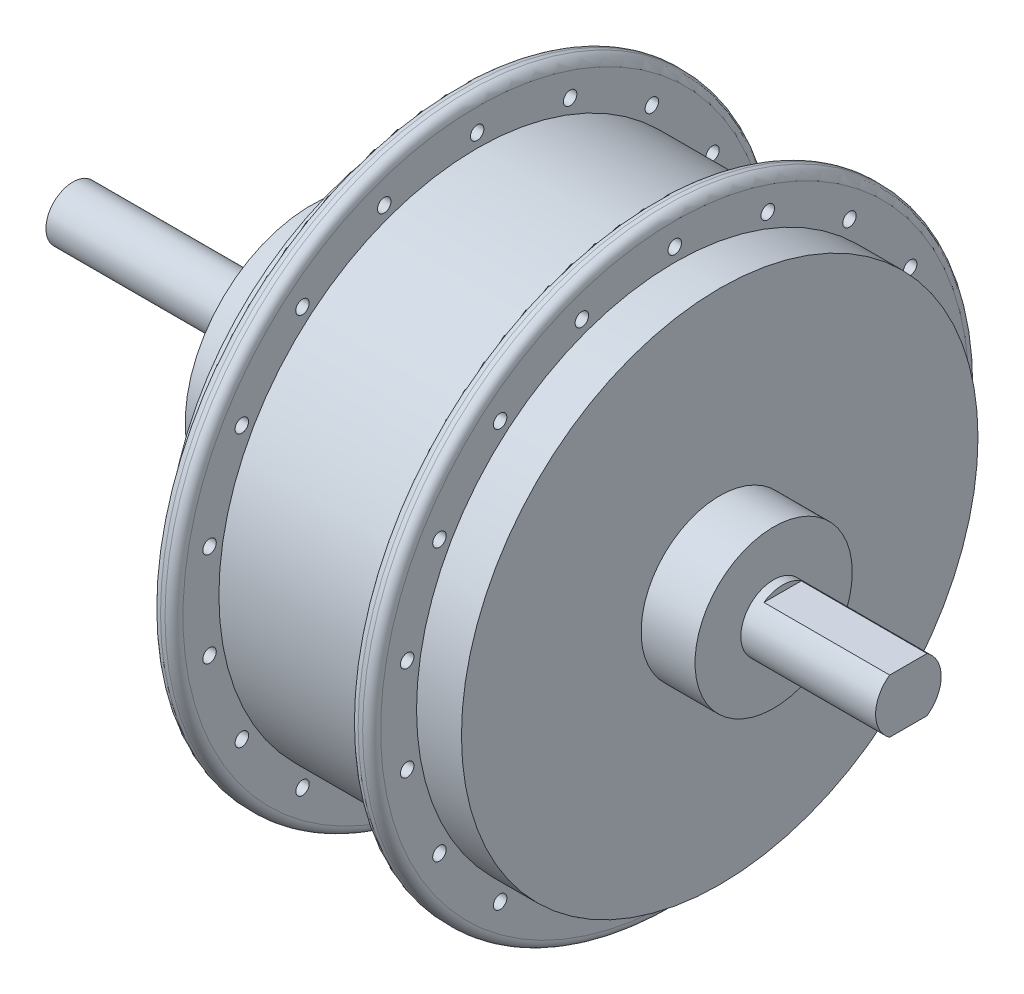
SolidWorks part; units mm, degrees
ref_plane "Спереди" through (0, 0, 0) normal (0, 0, 1) x (1, 0, 0)
ref_plane "Сверху" through (0, 0, 0) normal (0, 1, 0) x (1, 0, 0)
ref_plane "Справа" through (0, 0, 0) normal (1, 0, 0) x (0, 0, -1)
sketch "Эскиз1" plane through (0, 0, 0) normal (0, 0, 1) x (1, 0, 0)
  line L0 (27.6357, 0) -> (-114.9378, 0) construction
  line L1 (0, 0) -> (0, 7.3)
  line L2 (0, 7.3) -> (-30, 7.3)
  line L3 (-30, 7.3) -> (-30, 17.5)
  line L4 (-30, 17.5) -> (-42, 17.5)
  line L5 (-42, 17.5) -> (-42, 57.5)
  line L6 (-52, 67.5) -> (-57, 67.5)
  line L7 (-57, 67.5) -> (-57, 57.5)
  line L8 (-57, 57.5) -> (-96, 57.5)
  line L9 (-96, 57.5) -> (-96, 67.5)
  line L10 (-96, 67.5) -> (-101, 67.5)
  line L11 (-101, 67.5) -> (-101, 56)
  line L12 (-101, 56) -> (-109, 56)
  line L13 (-109, 56) -> (-109, 50)
  line L14 (-109, 50) -> (-121, 38)
  line L15 (-121, 38) -> (-121, 28)
  line L16 (-121, 28) -> (-133, 28)
  line L17 (-133, 28) -> (-133, 6)
  line L18 (-133, 6) -> (-186, 6)
  line L19 (-186, 6) -> (-186, 0)
  line L20 (-186, 0) -> (0, 0)
  line L21 (-52, 67.5) -> (-52, 57.5)
  line L22 (-52, 57.5) -> (-42, 57.5)
  point P24 (-101, 61.75)
  dimension "D1" = 14.6
  dimension "D2" = 35
  dimension "D3" = 135
  dimension "D4" = 10
  dimension "D5" = 112
  dimension "D6" = 100
  dimension "D7" = 76
  dimension "D8" = 56
  dimension "D9" = 12
  dimension "D10" = 59
  dimension "D11" = 5
  dimension "D12" = 103
  dimension "D13" = 12
  dimension "D14" = 53
  dimension "D15" = 10
  dimension "D16" = 8
  dimension "D17" = 12
  dimension "D18" = 12
  dimension "D19" = 30
  dimension "D20" = 67
  dimension "D21" = 79
  dimension "D22" = 10
  dimension "D23" = 5
revolve "Повернуть1" add sketch "Эскиз1" angle 360 about L0
fillet "Скругление1" radius 2 4 edges at (-101, 0, -67.5) (-96, 0, -67.5) (-57, 0, -67.5) (-52, 0, -67.5)
sketch "Эскиз2" plane through (-101, 0, 0) normal (-1, 0, 0) x (0, 0, 1)
  circle A0 centre (0, 60.5) radius 1.5
  circle A1 centre (20.6922, 56.8514) radius 1.5
  circle A2 centre (38.8887, 46.3457) radius 1.5
  circle A3 centre (52.3945, 30.25) radius 1.5
  circle A4 centre (59.5809, 10.5057) radius 1.5
  circle A5 centre (59.5809, -10.5057) radius 1.5
  circle A6 centre (52.3945, -30.25) radius 1.5
  circle A7 centre (38.8887, -46.3457) radius 1.5
  circle A8 centre (20.6922, -56.8514) radius 1.5
  circle A9 centre (0, -60.5) radius 1.5
  circle A10 centre (-20.6922, -56.8514) radius 1.5
  circle A11 centre (-38.8887, -46.3457) radius 1.5
  circle A12 centre (-52.3945, -30.25) radius 1.5
  circle A13 centre (-59.5809, -10.5057) radius 1.5
  circle A14 centre (-59.5809, 10.5057) radius 1.5
  circle A15 centre (-52.3945, 30.25) radius 1.5
  circle A16 centre (-38.8887, 46.3457) radius 1.5
  circle A17 centre (-20.6922, 56.8514) radius 1.5
  point P41 (0, 0)
  dimension "D2" = 3
  dimension "D1" = 59
  dimension "D3" = 18
extrude "Вырез-Вытянуть1" cut sketch "Эскиз2" against normal through all
sketch "Эскиз3" plane through (0, 0, 0) normal (1, 0, 0) x (0, 0, -1)
  line L1 (-26.3193, 6) -> (26.3193, 6)
  line L2 (-26.3193, 6) -> (-26.3193, -6)
  line L3 (-26.3193, -6) -> (26.3193, -6)
  line L4 (26.3193, 6) -> (26.3193, -6)
  line L5 (-26.3193, 6) -> (26.3193, -6) construction
  line L6 (-26.3193, -6) -> (26.3193, 6) construction
  point P0 (0, 0)
  dimension "D1" = 12
extrude "Вырез-Вытянуть2" cut sketch "Эскиз3" against normal blind 28 flip side to cut
